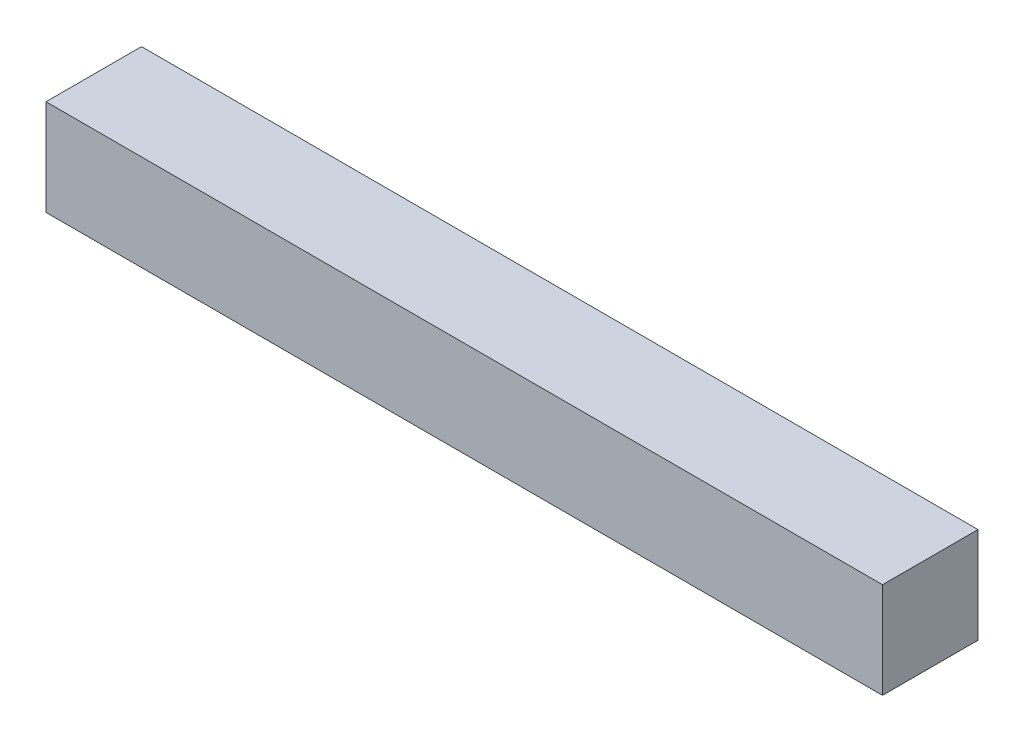
SolidWorks part; units mm, degrees
material "Cedar"
ref_plane "Front Plane" through (0, 0, 0) normal (0, 0, 1) x (1, 0, 0)
ref_plane "Top Plane" through (0, 0, 0) normal (0, 1, 0) x (1, 0, 0)
ref_plane "Right Plane" through (0, 0, 0) normal (1, 0, 0) x (0, 0, -1)
sketch "Sketch2" plane through (0, 0, 0) normal (1, 0, 0) x (0, 0, -1)
  line L1 (0, 0) -> (34.798, 0)
  line L2 (0, 0) -> (0, 34.925)
  line L3 (0, 34.925) -> (34.798, 34.925)
  line L4 (34.798, 0) -> (34.798, 34.925)
  dimension "D1" = 34.798
  dimension "D2" = 34.925
extrude "Boss-Extrude1" add sketch "Sketch2" along normal blind 304.8
